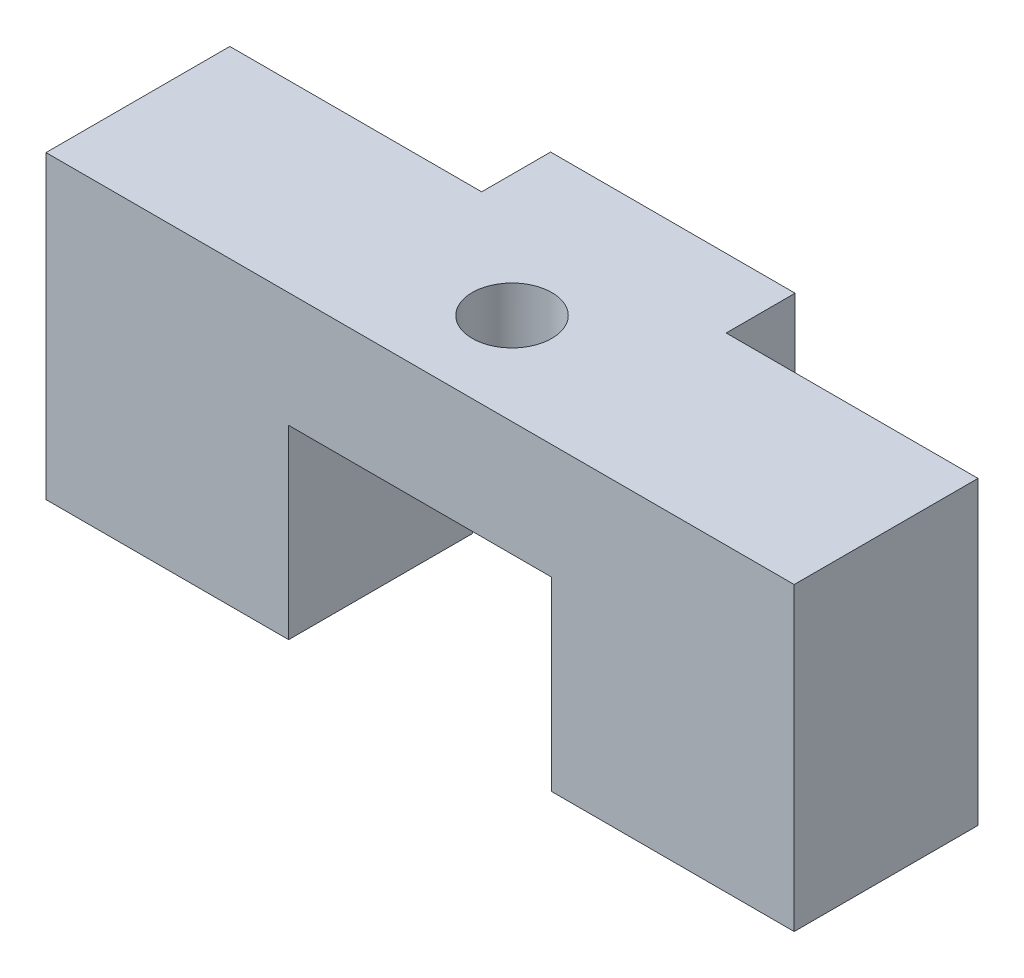
SolidWorks part; units mm, degrees
ref_plane "Front Plane" through (0, 0, 0) normal (0, 0, 1) x (1, 0, 0)
ref_plane "Top Plane" through (0, 0, 0) normal (0, 1, 0) x (1, 0, 0)
ref_plane "Right Plane" through (0, 0, 0) normal (1, 0, 0) x (0, 0, -1)
sketch "Sketch1" plane through (0, 0, 0) normal (0, 1, 0) x (1, 0, 0)
  line L0 (10.3378, 0) -> (10.3378, -9.5839) construction
  line L1 (0, 0) -> (20.6756, 0)
  line L2 (0, 0) -> (0, 5.08)
  line L3 (13.716, 5.08) -> (20.6756, 5.08)
  line L4 (20.6756, 0) -> (20.6756, 5.08)
  line L5 (6.9596, 5.08) -> (6.9596, 6.985)
  line L6 (6.9596, 6.985) -> (13.716, 6.985)
  line L7 (13.716, 6.985) -> (13.716, 5.08)
  line L8 (0, 5.08) -> (6.9596, 5.08)
  point P9 (10.3378, 6.985)
  dimension "D1" = 5.08
  dimension "D2" = 20.6756
  dimension "D3" = 6.7564
  dimension "D4" = 1.905
extrude "Boss-Extrude1" add sketch "Sketch1" along normal blind 3.175 contours L8 L5 L6 L7 L3 L4 L1 L2
sketch "Sketch2" plane through (0, 0, 0) normal (0, -1, 0) x (1, 0, 0)
  line L0 (13.716, -5.08) -> (20.6756, -5.08) construction
  line L1 (20.6756, 0) -> (13.97, 0)
  line L2 (20.6756, 0) -> (20.6756, -5.08)
  line L3 (20.6756, -5.08) -> (13.97, -5.08)
  line L4 (13.97, 0) -> (13.97, -5.08)
  line L5 (0, 0) -> (20.6756, 0) construction
  line L6 (0, -5.08) -> (6.7056, -5.08)
  line L7 (0, -5.08) -> (0, 0)
  line L8 (0, 0) -> (6.7056, 0)
  line L9 (6.7056, -5.08) -> (6.7056, 0)
  line L10 (6.7056, 0) -> (13.97, 0) construction
  line L11 (10.3378, 0) -> (10.3378, 5.3366) construction
  line L12 (10.3378, -6.985) -> (10.3378, -8.8295) construction
  line L13 (6.9596, -6.985) -> (13.716, -6.985) construction
  dimension "D1" = 7.2644
extrude "Boss-Extrude2" add sketch "Sketch2" along normal blind 5.1308
hole_wizard "M2 Clearance Hole1" positions "Sketch3" profile "Sketch4" hole size "M2" standard "ANSI Metric" end condition through all
sketch "Sketch3" plane through (0, 3.175, 0) normal (0, 1, 0) x (1, 0, 0)
  line L0 (10.3378, 0) -> (10.3378, -3.1464) construction
  line L1 (0, 0) -> (20.6756, 0) construction
  line L4 (20.6756, 2.54) -> (26.814, 2.54) construction
  line L5 (20.6756, 0) -> (20.6756, 5.08) construction
  point P0 (10.3378, 2.54)
sketch "Sketch4" plane through (10.3378, 3.175, -2.54) normal (1, 0, 0) x (0, 0, 1)
  line L0 (0, 0) -> (0, 8.3058)
  line L1 (0, 8.3058) -> (1.1, 8.3058)
  line L2 (1.1, 8.3058) -> (1.1, 0)
  line L5 (1.1, 0) -> (0, 0)
  line L11 (0, -6.35) -> (0, 107.95) construction
  dimension "Thru Hole Dia." = 2.2
  dimension "Thru Hole Depth" = 8.3058
